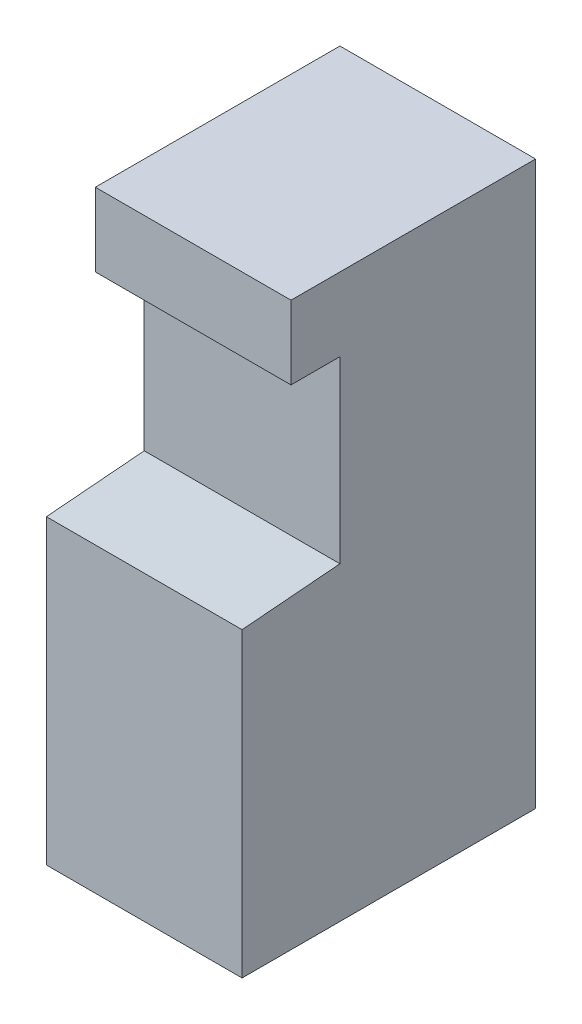
SolidWorks part; units mm, degrees
ref_plane "Front Plane" through (0, 0, 0) normal (0, 0, 1) x (1, 0, 0)
ref_plane "Top Plane" through (0, 0, 0) normal (0, 1, 0) x (1, 0, 0)
ref_plane "Right Plane" through (0, 0, 0) normal (1, 0, 0) x (0, 0, -1)
sketch "Sketch1" plane through (0, 0, 0) normal (0, 1, 0) x (1, 0, 0)
  line L1 (0, 0) -> (609.6, 0)
  line L2 (0, 0) -> (0, -914.4)
  line L3 (0, -914.4) -> (609.6, -914.4)
  line L4 (609.6, 0) -> (609.6, -914.4)
extrude "Boss-Extrude1" add sketch "Sketch1" along normal blind 939.8
sketch "Sketch2" plane through (0, 939.8, 0) normal (0, 1, 0) x (1, 0, 0)
  line L0 (609.6, -914.4) -> (609.6, 0) construction
  line L1 (0, -914.4) -> (609.6, -914.4)
  line L2 (0, -914.4) -> (0, -609.6)
  line L3 (0, -609.6) -> (609.6, -609.6)
  line L4 (609.6, -914.4) -> (609.6, -609.6)
extrude "Boss-Extrude2" add sketch "Sketch2" along normal blind 25.4
sketch "Sketch3" plane through (0, 0, 0) normal (-1, 0, 0) x (0, 0, 1)
  line L0 (914.4, 965.2) -> (914.4, 0) construction
  line L1 (609.6, 965.2) -> (914.4, 965.2) construction
  line L2 (609.6, 965.2) -> (609.6, 939.8) construction
  line L3 (609.6, 939.8) -> (914.4, 939.8) construction
  line L4 (914.4, 965.2) -> (914.4, 939.8) construction
  line L5 (0, 939.8) -> (609.6, 939.8) construction
  line L6 (609.6, 965.2) -> (914.4, 939.8)
  line L7 (914.4, 939.8) -> (914.4, 965.2)
  line L8 (914.4, 965.2) -> (609.6, 965.2)
extrude "Cut-Extrude1" cut sketch "Sketch3" against normal through all
sketch "Sketch4" plane through (0, 939.8, 0) normal (0, 1, 0) x (1, 0, 0)
  line L1 (609.6, 0) -> (0, 0)
  line L2 (609.6, 0) -> (609.6, -609.6)
  line L3 (609.6, -609.6) -> (0, -609.6)
  line L4 (0, 0) -> (0, -609.6)
extrude "Boss-Extrude3" add sketch "Sketch4" along normal up to vertex (76.2 mm away)
sketch "Sketch5" plane through (0, 965.2, 0) normal (0, 1, 0) x (1, 0, 0)
  line L1 (0, 0) -> (609.6, 0)
  line L2 (0, 0) -> (0, -609.6)
  line L3 (0, -609.6) -> (609.6, -609.6)
  line L4 (609.6, 0) -> (609.6, -609.6)
extrude "Boss-Extrude4" add sketch "Sketch5" along normal blind 558.8
sketch "Sketch6" plane through (0, 1524, 0) normal (0, 1, 0) x (1, 0, 0)
  line L1 (0, 0) -> (609.6, 0)
  line L2 (0, 0) -> (0, -609.6)
  line L3 (0, -609.6) -> (609.6, -609.6)
  line L4 (609.6, 0) -> (609.6, -609.6)
extrude "Boss-Extrude5" add sketch "Sketch6" along normal blind 228.6
sketch "Sketch7" plane through (0, 0, 609.6) normal (0, 0, 1) x (1, 0, 0)
  line L1 (0, 1752.6) -> (609.6, 1752.6)
  line L2 (0, 1752.6) -> (0, 1524)
  line L3 (0, 1524) -> (609.6, 1524)
  line L4 (609.6, 1752.6) -> (609.6, 1524)
extrude "Boss-Extrude6" add sketch "Sketch7" along normal blind 152.4
